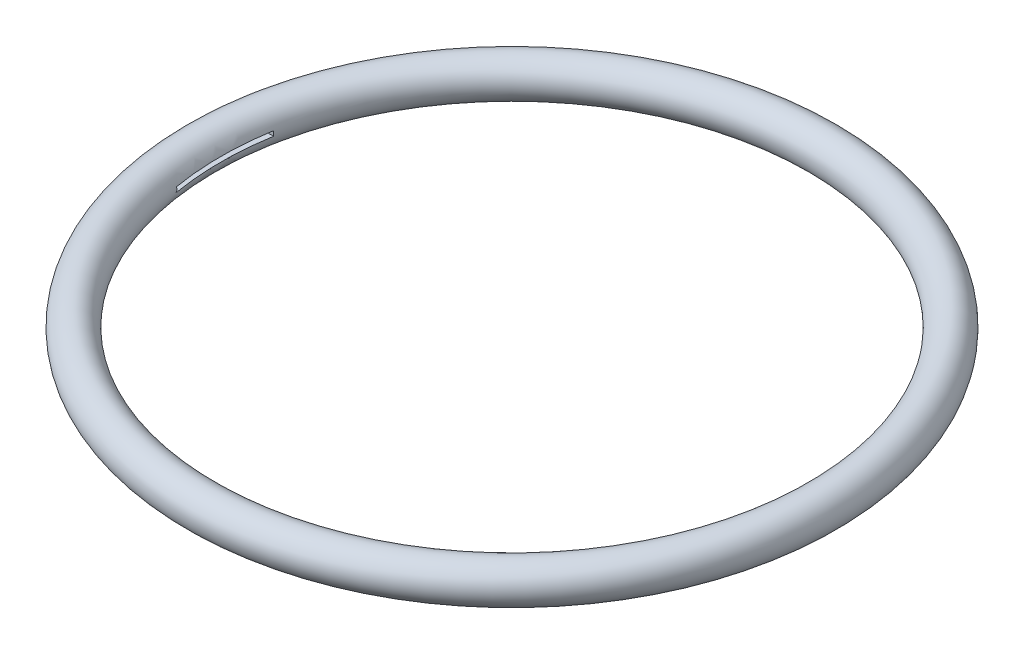
SolidWorks part; units mm, degrees
ref_plane "Front Plane" through (0, 0, 0) normal (0, 0, 1) x (1, 0, 0)
ref_plane "Top Plane" through (0, 0, 0) normal (0, 1, 0) x (1, 0, 0)
ref_plane "Right Plane" through (0, 0, 0) normal (1, 0, 0) x (0, 0, -1)
sketch "Sketch1" plane through (0, 0, 0) normal (0, 0, 1) x (1, 0, 0)
  line L0 (32, 4.0904) -> (32, -6.6909) construction
  circle A0 centre (0, 0) radius 2
  circle A1 centre (0, 0) radius 1
  dimension "D1" = 2
  dimension "D2" = 4
  dimension "D3" = 30
revolve "Revolve1" add sketch "Sketch1" angle 360 about L0
sketch "Sketch2" plane through (0, 0, 0) normal (0, 0, 1) x (1, 0, 0)
  circle A1 centre (0.5, 0) radius 1
  dimension "D1" = 2
  dimension "D2" = 0.5
extrude "Cut-Extrude1" cut sketch "Sketch2" against normal mid plane 12 contours A1
sketch "Sketch3" plane through (0, 0, 0) normal (1, 0, 0) x (0, 0, -1)
  line L1 (-5, 0.25) -> (5, 0.25)
  line L2 (-5, 0.25) -> (-5, -0.25)
  line L3 (-5, -0.25) -> (5, -0.25)
  line L4 (5, 0.25) -> (5, -0.25)
  line L5 (-5, 0.25) -> (5, -0.25) construction
  line L6 (-5, -0.25) -> (5, 0.25) construction
  point P0 (0, 0)
  dimension "D1" = 10
  dimension "D2" = 0.5
extrude "Cut-Extrude2" cut sketch "Sketch3" along normal up to next
